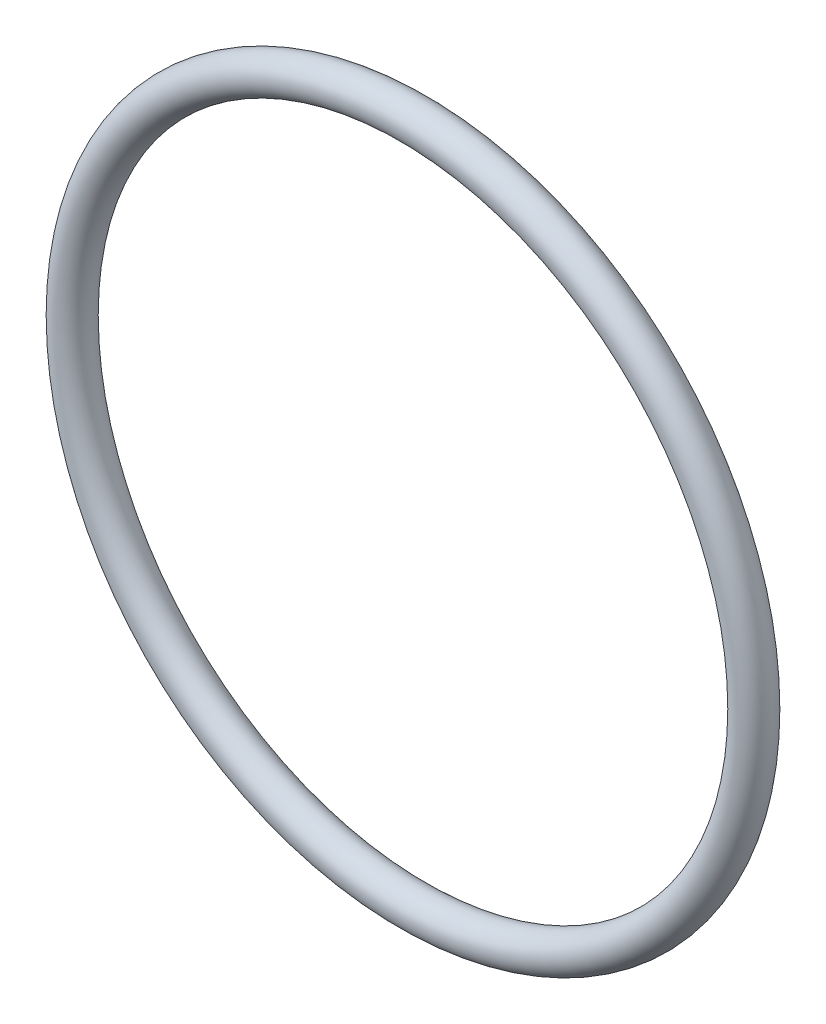
SolidWorks part; units mm, degrees
ref_plane "Front Plane" through (0, 0, 0) normal (0, 0, 1) x (1, 0, 0)
ref_plane "Top Plane" through (0, 0, 0) normal (0, 1, 0) x (1, 0, 0)
ref_plane "Right Plane" through (0, 0, 0) normal (1, 0, 0) x (0, 0, -1)
sketch "Sketch1" plane through (0, 0, 0) normal (1, 0, 0) x (0, 0, -1)
  line L0 (-1.694, 0) -> (1.694, 0) construction
  circle A0 centre (0, 18.5) radius 1
  point P8 (0, 0)
  dimension "D1" = 2
  dimension "D2" = 37
revolve "Revolve1" add sketch "Sketch1" angle 360 about L0
